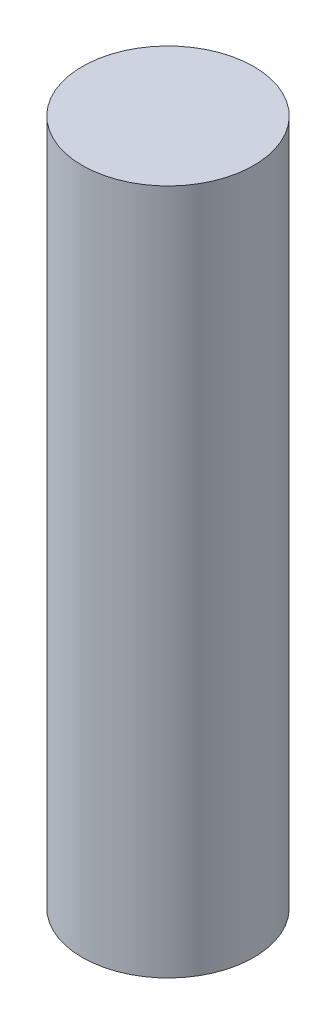
SolidWorks part; units mm, degrees
ref_plane "Ebene vorne" through (0, 0, 0) normal (0, 0, 1) x (1, 0, 0)
ref_plane "Ebene oben" through (0, 0, 0) normal (0, 1, 0) x (1, 0, 0)
ref_plane "Ebene rechts" through (0, 0, 0) normal (1, 0, 0) x (0, 0, -1)
sketch "Sketch1" plane through (0, 0, 0) normal (0, 1, 0) x (1, 0, 0)
  circle A0 centre (0, 0) radius 25
  dimension "D1" = 50
extrude "Boss-Extrude1" add sketch "Sketch1" along normal mid plane 200
